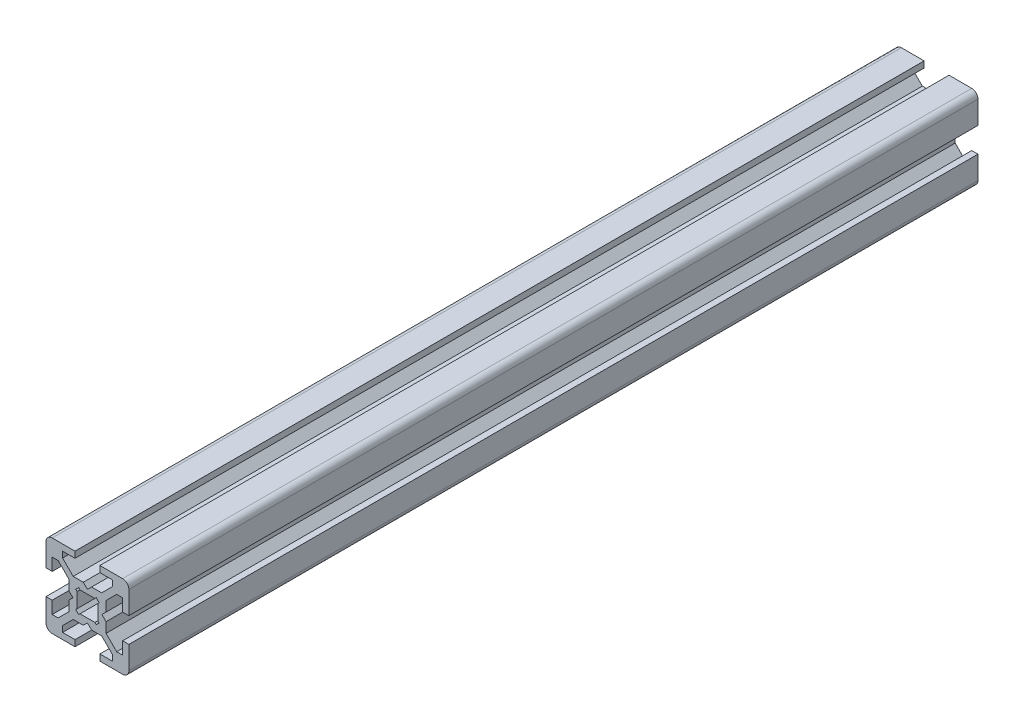
SolidWorks part; units mm, degrees
ref_plane "Front Plane" through (0, 0, 0) normal (0, 0, 1) x (1, 0, 0)
ref_plane "Top Plane" through (0, 0, 0) normal (0, 1, 0) x (1, 0, 0)
ref_plane "Right Plane" through (0, 0, 0) normal (1, 0, 0) x (0, 0, -1)
sketch "Sketch1" plane through (0, 0, 0) normal (0, 0, 1) x (1, 0, 0)
  line L0 (0, -1000) -> (0, 49000) construction
  line L1 (-1000, 0) -> (49000, 0) construction
  line L2 (0, 3.5) -> (1, 4.5)
  line L3 (1, 4.5) -> (3.4393, 4.5)
  line L4 (3.4393, 4.5) -> (6, 7.0607)
  line L5 (6, 7.0607) -> (6, 8.5)
  line L6 (6, 8.5) -> (3, 8.5)
  line L7 (3, 8.5) -> (3, 10)
  line L8 (3, 10) -> (10, 10)
  line L9 (0, 0) -> (35355.3391, 35355.3391) construction
  line L10 (-1.7929, 2.5) -> (1.7929, 2.5)
  line L11 (1.7929, 2.5) -> (2.1213, 2.8284)
  line L12 (2.1213, 2.8284) -> (2.8284, 2.1213)
  line L13 (2.5, 1.7929) -> (2.8284, 2.1213)
  line L14 (2.5, -1.7929) -> (2.5, 1.7929)
  line L15 (3.5, 0) -> (4.5, 1)
  line L16 (4.5, 1) -> (4.5, 3.4393)
  line L17 (4.5, 3.4393) -> (7.0607, 6)
  line L18 (7.0607, 6) -> (8.5, 6)
  line L19 (8.5, 6) -> (8.5, 3)
  line L20 (8.5, 3) -> (10, 3)
  line L21 (10, 3) -> (10, 10)
  line L22 (-3.5, 0) -> (-4.5, 1)
  line L23 (-2.5, -1.7929) -> (-2.5, 1.7929)
  line L24 (0, 3.5) -> (-1, 4.5)
  line L25 (-10, 3) -> (-10, 10)
  line L26 (-8.5, 3) -> (-10, 3)
  line L27 (-8.5, 6) -> (-8.5, 3)
  line L28 (-7.0607, 6) -> (-8.5, 6)
  line L29 (-4.5, 3.4393) -> (-7.0607, 6)
  line L30 (-4.5, 1) -> (-4.5, 3.4393)
  line L31 (-2.5, 1.7929) -> (-2.8284, 2.1213)
  line L32 (-2.1213, 2.8284) -> (-2.8284, 2.1213)
  line L33 (-1.7929, 2.5) -> (-2.1213, 2.8284)
  line L34 (-3, 10) -> (-10, 10)
  line L35 (-3, 8.5) -> (-3, 10)
  line L36 (-6, 8.5) -> (-3, 8.5)
  line L37 (-6, 7.0607) -> (-6, 8.5)
  line L38 (-3.4393, 4.5) -> (-6, 7.0607)
  line L39 (-1, 4.5) -> (-3.4393, 4.5)
  line L40 (8.5, -3) -> (10, -3)
  line L41 (8.5, -6) -> (8.5, -3)
  line L42 (7.0607, -6) -> (8.5, -6)
  line L43 (10, -3) -> (10, -10)
  line L44 (3, -10) -> (10, -10)
  line L45 (3, -8.5) -> (3, -10)
  line L46 (-3, -8.5) -> (-3, -10)
  line L47 (6, -8.5) -> (3, -8.5)
  line L48 (6, -7.0607) -> (6, -8.5)
  line L49 (3.4393, -4.5) -> (6, -7.0607)
  line L50 (4.5, -3.4393) -> (7.0607, -6)
  line L51 (4.5, -1) -> (4.5, -3.4393)
  line L52 (3.5, 0) -> (4.5, -1)
  line L53 (2.5, -1.7929) -> (2.8284, -2.1213)
  line L54 (2.1213, -2.8284) -> (2.8284, -2.1213)
  line L55 (1.7929, -2.5) -> (2.1213, -2.8284)
  line L56 (1, -4.5) -> (3.4393, -4.5)
  line L57 (0, -3.5) -> (1, -4.5)
  line L58 (-1, -4.5) -> (-3.4393, -4.5)
  line L59 (-3.4393, -4.5) -> (-6, -7.0607)
  line L60 (-6, -7.0607) -> (-6, -8.5)
  line L61 (-6, -8.5) -> (-3, -8.5)
  line L62 (-3, -10) -> (-10, -10)
  line L63 (-10, -3) -> (-10, -10)
  line L64 (-8.5, -3) -> (-10, -3)
  line L65 (-8.5, -6) -> (-8.5, -3)
  line L66 (-7.0607, -6) -> (-8.5, -6)
  line L67 (-4.5, -3.4393) -> (-7.0607, -6)
  line L68 (-4.5, -1) -> (-4.5, -3.4393)
  line L69 (-3.5, 0) -> (-4.5, -1)
  line L70 (-2.5, -1.7929) -> (-2.8284, -2.1213)
  line L71 (-2.1213, -2.8284) -> (-2.8284, -2.1213)
  line L72 (-1.7929, -2.5) -> (-2.1213, -2.8284)
  line L73 (-1.7929, -2.5) -> (1.7929, -2.5)
  line L74 (0, -3.5) -> (-1, -4.5)
  point P18 (2.4749, 2.4749)
  point P19 (4.5, 8.5)
  point P35 (0, 2.5)
  point P64 (2.5, 0)
  point P81 (-2.5, 0)
  dimension "D2" = 20
  dimension "D3" = 7
  dimension "D4" = 1.5
  dimension "D5" = 1.5
  dimension "D6" = 4
  dimension "D7" = 1
  dimension "D8" = 9
  dimension "D9" = 5
  dimension "D10" = 1
  dimension "D11" = 3.5
extrude "Boss-Extrude1" add sketch "Sketch1" along normal blind 205
fillet "Fillet1" radius 1.5 4 edges at (-10, -10, 102.5) (10, -10, 102.5) (10, 10, 102.5) (-10, 10, 102.5)
